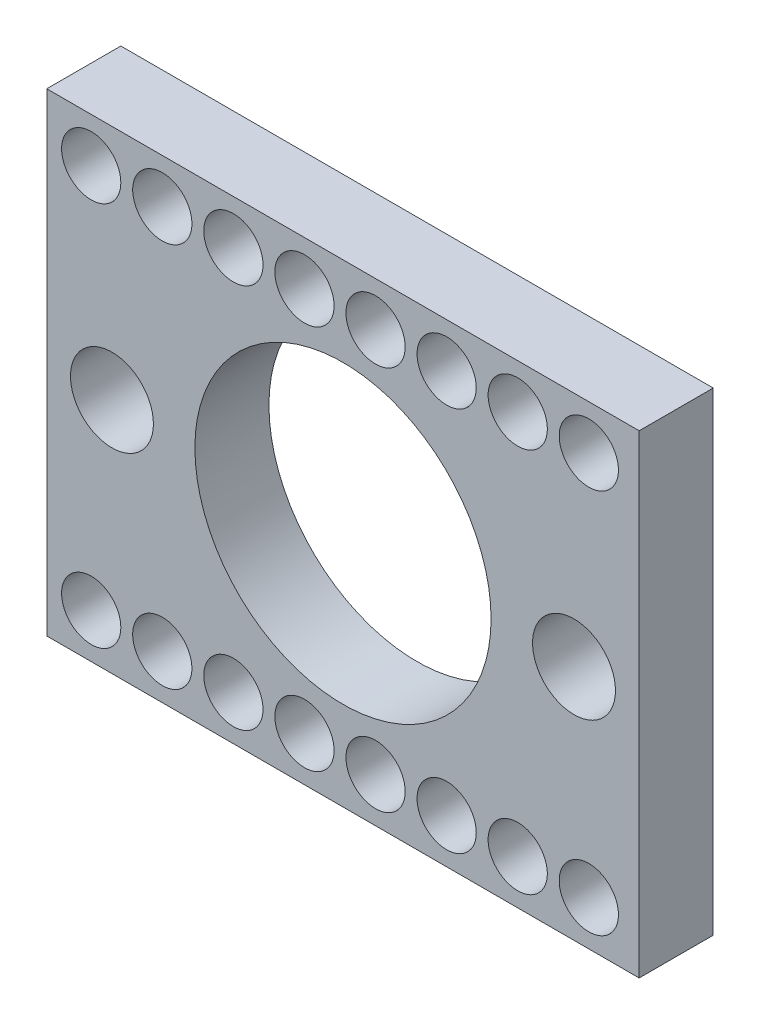
SolidWorks part; units mm, degrees
material "Copper"
ref_plane "Front Plane" through (0, 0, 0) normal (0, 0, 1) x (1, 0, 0)
ref_plane "Top Plane" through (0, 0, 0) normal (0, 1, 0) x (1, 0, 0)
ref_plane "Right Plane" through (0, 0, 0) normal (1, 0, 0) x (0, 0, -1)
sketch "Sketch2" plane through (0, 0, 0) normal (0, 0, 1) x (1, 0, 0)
  line L1 (9.1141, -7.62) -> (-11.2059, -7.62)
  line L2 (9.1141, -7.62) -> (9.1141, 7.62)
  line L3 (9.1141, 7.62) -> (-11.2059, 7.62)
  line L4 (-11.2059, -7.62) -> (-11.2059, 7.62)
  line L5 (9.1141, -7.62) -> (-11.2059, 7.62) construction
  line L6 (9.1141, 7.62) -> (-11.2059, -7.62) construction
  line L7 (11.6541, -10.16) -> (-13.7459, -10.16)
  line L8 (11.6541, -10.16) -> (11.6541, 10.16)
  line L9 (11.6541, 10.16) -> (-13.7459, 10.16)
  line L10 (-13.7459, -10.16) -> (-13.7459, 10.16)
  line L11 (11.6541, -10.16) -> (-13.7459, 10.16) construction
  line L12 (11.6541, 10.16) -> (-13.7459, -10.16) construction
  circle A0 centre (-1.0459, 0) radius 6.35
  circle A1 centre (-10.9519, 0) radius 1.778
  circle A2 centre (8.8601, 0) radius 1.778
  point P0 (-1.0459, 0)
  point P15 (0, 0)
  dimension "D3" = 12.7
  dimension "D6" = 3.556
  dimension "D7" = 3.556
  dimension "D1" = 15.24
  dimension "D2" = 20.32
  dimension "D4" = 9.906
  dimension "D5" = 9.906
  dimension "D8" = 20.32
  dimension "D9" = 25.4
extrude "Boss-Extrude1" add sketch "Sketch2" along normal blind 3.175 contours A2 L2 L3 L4 A1 L1 A0 | L10 L7 L8 L9 A2 L2 L1 L4 A1 L3
sketch "Sketch4" plane through (0, 0, 3.175) normal (0, 0, 1) x (1, 0, 0)
  line L0 (-13.7459, -10.16) -> (-13.7459, 10.16) construction
  line L2 (11.6541, 10.16) -> (-13.7459, 10.16) construction
  line L3 (11.6541, -10.16) -> (-13.7459, -10.16) construction
  circle A0 centre (-11.8409, 8.255) radius 1.27
  circle A1 centre (-8.7929, 8.255) radius 1.27
  circle A2 centre (-5.7449, 8.255) radius 1.27
  circle A3 centre (-2.6969, 8.255) radius 1.27
  circle A4 centre (0.3511, 8.255) radius 1.27
  circle A5 centre (3.3991, 8.255) radius 1.27
  circle A6 centre (6.4471, 8.255) radius 1.27
  circle A7 centre (9.4951, 8.255) radius 1.27
  circle A8 centre (-11.8409, -8.255) radius 1.27
  circle A9 centre (-8.7929, -8.255) radius 1.27
  circle A10 centre (-5.7449, -8.255) radius 1.27
  circle A11 centre (-2.6969, -8.255) radius 1.27
  circle A12 centre (0.3511, -8.255) radius 1.27
  circle A13 centre (3.3991, -8.255) radius 1.27
  circle A14 centre (6.4471, -8.255) radius 1.27
  circle A15 centre (9.4951, -8.255) radius 1.27
  dimension "D1" = 2.54
  dimension "D5" = 2.54
  dimension "D2" = 1.905
  dimension "D3" = 1.905
  dimension "D6" = 1.905
  dimension "D7" = 1.905
  dimension "D4" = 8
  dimension "D8" = 8
extrude "Cut-Extrude1" cut sketch "Sketch4" against normal blind 3.175
